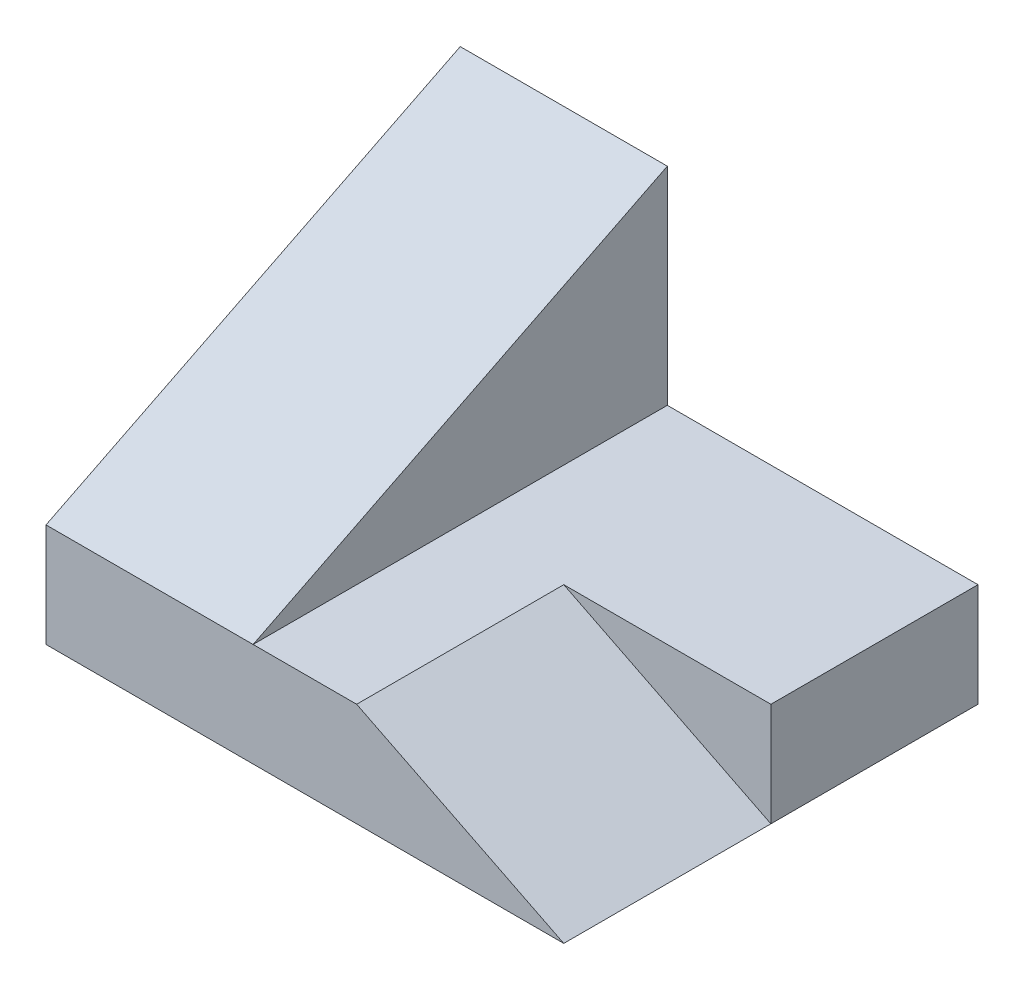
SolidWorks part; units mm, degrees
ref_plane "Front Plane" through (0, 0, 0) normal (0, 0, 1) x (1, 0, 0)
ref_plane "Top Plane" through (0, 0, 0) normal (0, 1, 0) x (1, 0, 0)
ref_plane "Right Plane" through (0, 0, 0) normal (1, 0, 0) x (0, 0, -1)
sketch "Sketch1" plane through (0, 0, 0) normal (0, 0, 1) x (1, 0, 0)
  line L0 (-63.5, 76.2) -> (-12.7, 76.2)
  line L1 (-12.7, 76.2) -> (-12.7, 25.4)
  line L2 (-12.7, 25.4) -> (63.5, 25.4)
  line L3 (63.5, 25.4) -> (63.5, 0)
  line L4 (63.5, 0) -> (-63.5, 0)
  line L5 (-63.5, 0) -> (-63.5, 76.2)
  dimension "D1" = 50.8
  dimension "D2" = 50.8
  dimension "D3" = 76.2
  dimension "D4" = 25.4
extrude "Boss-Extrude1" add sketch "Sketch1" along normal blind 101.6
sketch "Sketch2" plane through (-12.7, 0, 0) normal (1, 0, 0) x (0, 0, -1)
  line L0 (0, 76.2) -> (-101.6, 25.4)
extrude "Cut-Extrude2" cut sketch "Sketch2" against normal through all and the other way through all flip side to cut
sketch "Sketch3" plane through (0, 0, 101.6) normal (0, 0, 1) x (1, 0, 0)
  line L0 (12.7, 25.4) -> (63.5, 25.4)
  line L1 (63.5, 0) -> (12.7, 0)
  line L2 (-63.5, 0) -> (63.5, 0) construction
  line L3 (12.7, 0) -> (12.7, 25.4)
  line L4 (63.5, 25.4) -> (-12.7, 25.4) construction
  line L5 (12.7, 25.4) -> (63.5, 0)
  line L6 (63.5, 25.4) -> (63.5, 0)
  line M2 (63.5, 25.4) -> (-12.7, 25.4)
  line M6 (63.5, 0) -> (63.5, 25.4)
  dimension "D1" = 50.8
extrude "Cut-Extrude6" cut sketch "Sketch3" against normal blind 50.8 contours L5 M2 M6
